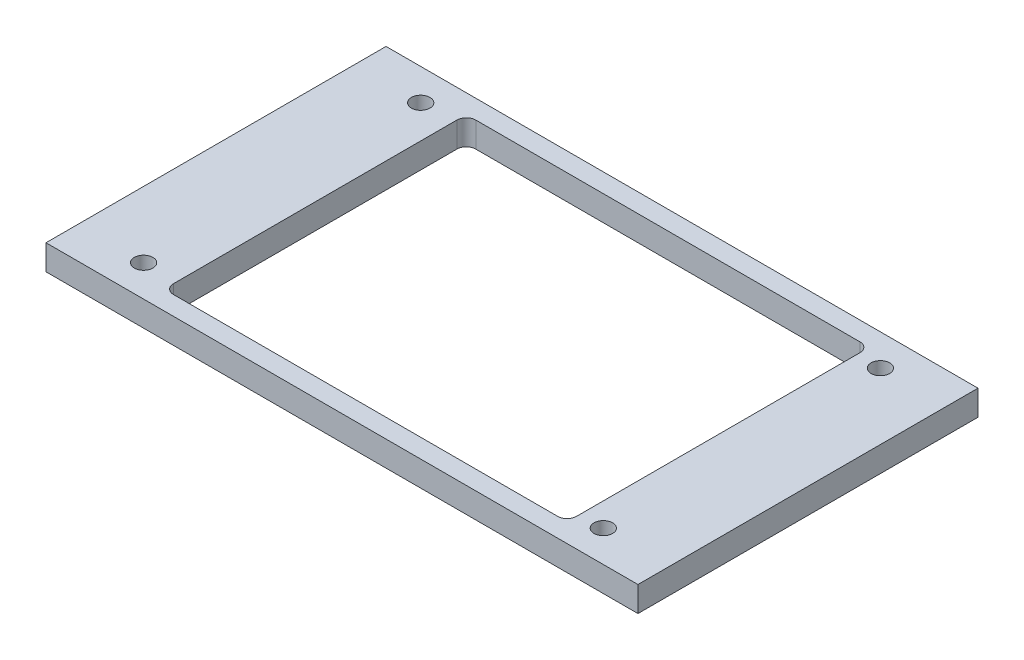
SolidWorks part; units mm, degrees
material "Стекло кварцевое прозрачное"
ref_plane "Спереди" through (0, 0, 0) normal (0, 0, 1) x (1, 0, 0)
ref_plane "Сверху" through (0, 0, 0) normal (0, 1, 0) x (1, 0, 0)
ref_plane "Справа" through (0, 0, 0) normal (1, 0, 0) x (0, 0, -1)
sketch "Эскиз1" plane through (0, 0, 0) normal (0, 1, 0) x (1, 0, 0)
  line L1 (-94, -54) -> (94, -54)
  line L2 (-94, -54) -> (-94, 54)
  line L3 (-94, 54) -> (94, 54)
  line L4 (94, -54) -> (94, 54)
  line L5 (-94, -54) -> (94, 54) construction
  line L6 (-94, 54) -> (94, -54) construction
  point P0 (0, 0)
  dimension "D1" = 188
  dimension "D2" = 108
extrude "Бобышка-Вытянуть1" add sketch "Эскиз1" along normal blind 8
sketch "Эскиз2" plane through (0, 8, 0) normal (0, 1, 0) x (1, 0, 0)
  line L0 (94, 54) -> (-94, 54) construction
  line L1 (-62.5, -48) -> (65.5, -48)
  line L2 (-62.5, -48) -> (-62.5, 48)
  line L3 (-62.5, 48) -> (65.5, 48)
  line L4 (65.5, -48) -> (65.5, 48)
  line L5 (-62.5, -48) -> (65.5, 48) construction
  line L6 (-62.5, 48) -> (65.5, -48) construction
  line L7 (-94, -54) -> (94, -54) construction
  line L8 (-94, 54) -> (-94, -54) construction
  line L9 (94, -54) -> (94, 54) construction
  circle A0 centre (-73, 44) radius 2.95
  circle A1 centre (73, 44) radius 2.95
  circle A2 centre (-73, -44) radius 2.95
  circle A3 centre (73, -44) radius 2.95
  dimension "D7" = 5.9
  dimension "D1" = 6
  dimension "D2" = 6
  dimension "D3" = 31.5
  dimension "D4" = 28.5
  dimension "D9" = 44
  dimension "D10" = 73
  dimension "D11" = 44
  dimension "D12" = 44
  dimension "D13" = 73
  dimension "D14" = 44
  dimension "D15" = 73
  dimension "D16" = 73
extrude "Вырез-Вытянуть1" cut sketch "Эскиз2" against normal through all
fillet "Скругление1" radius 3 4 edges at (65.5, 4, 48) (65.5, 4, -48) (-62.5, 4, 48) (-62.5, 4, -48)
